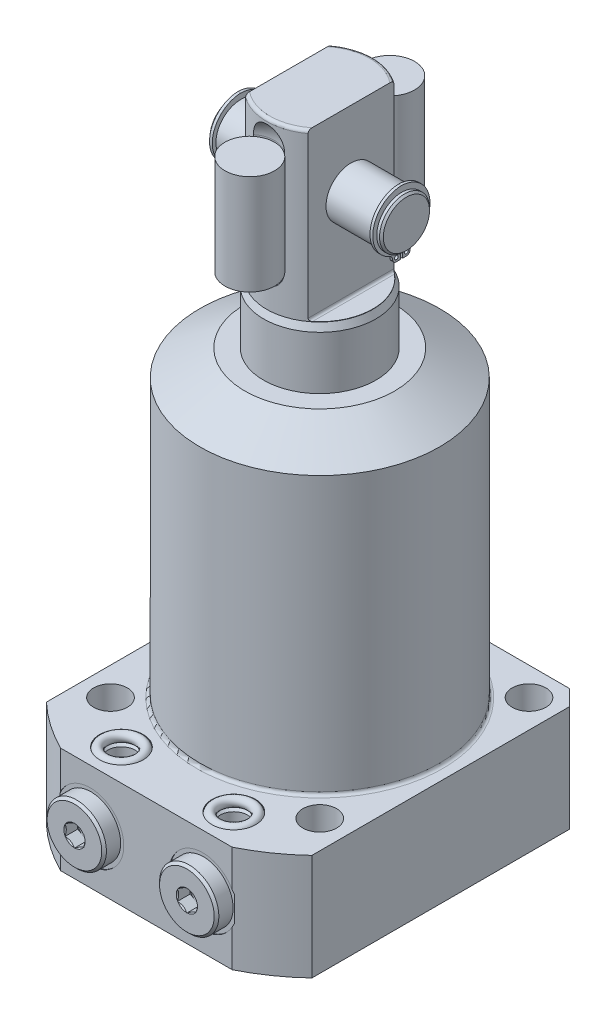
SolidWorks part; units mm, degrees
material "AISI 1020"
ref_plane "Front Plane" through (0, 0, 0) normal (0, 0, 1) x (1, 0, 0)
ref_plane "Top Plane" through (0, 0, 0) normal (0, 1, 0) x (1, 0, 0)
ref_plane "Right Plane" through (0, 0, 0) normal (1, 0, 0) x (0, 0, -1)
sketch "Sketch1" plane through (0, 0, 0) normal (0, 0, 1) x (1, 0, 0)
  line L0 (18, 0) -> (18, 114)
  line L1 (18, 114) -> (17, 116.1445)
  line L2 (17, 116.1445) -> (17, 168.25)
  line L3 (16, 169.25) -> (0, 169.25)
  line L4 (0, 61.9815) -> (0, 93.5758) construction
  line L8 (0, -3.075) -> (0, 64.575) construction
  line L9 (18, 0) -> (0, 0)
  line L10 (0, 0) -> (0, 169.25)
  line L11 (-25.0821, -34) -> (21.8096, -34) construction
  arc A0 (17, 168.25) -> (16, 169.25) centre (16, 168.25) ccw
  dimension "D1" = 1
  dimension "D2" = 36
  dimension "D3" = 34
  dimension "D4" = 55.25
  dimension "D5" = 34
  dimension "D6" = 25
  dimension "D7" = 203.25
revolve "PLUNGER" add sketch "Sketch1" angle 360 about L8
ref_plane "FLAT_SKTCH_PLN" through (0, 0, 0) normal (0, 0, 1) x (1, 0, 0)
sketch "Sketch17" plane through (0, 0, 0) normal (0, 0, 1) x (1, 0, 0)
  line L0 (16, 169.25) -> (-16, 169.25) construction
  line L1 (17, 116.1445) -> (17, 168.25) construction
  line L2 (16, 169.25) -> (-16, 169.25)
  line L3 (17, 116.1445) -> (17, 168.25)
  line L5 (10, 169.25) -> (17, 169.25)
  line L6 (10, 169.25) -> (10, 117.05)
  line L7 (10.8, 116.25) -> (17, 116.25)
  line L8 (17, 169.25) -> (17, 116.25)
  line L9 (0, 168.25) -> (0, 116.1445) construction
  line L10 (0, 57.0947) -> (0, 92.2162) construction
  line L11 (0, 114) -> (0, 0) construction
  line L12 (0, 114) -> (0, 116.1445) construction
  line L13 (-17, 169.25) -> (-17, 116.25)
  line L14 (-10.8, 116.25) -> (-17, 116.25)
  line L15 (-10, 169.25) -> (-10, 117.05)
  line L16 (-10, 169.25) -> (-17, 169.25)
  line L17 (-17, 116.1445) -> (-17, 168.25)
  arc A0 (10, 117.05) -> (10.8, 116.25) centre (10.8, 117.05) ccw
  arc A1 (-10, 117.05) -> (-10.8, 116.25) centre (-10.8, 117.05) cw
  dimension "D3" = 0.8
  dimension "D1" = 53
  dimension "D2" = 20
extrude "FLATS" cut sketch "Sketch17" against normal mid plane 100 contours L6 A0 L7 L8 L5 | L13 L14 A1 L15 L16
sketch "Sketch22" plane through (0, 0, 0) normal (0, 0, 1) x (1, 0, 0)
  line L0 (-11.5689, 145.25) -> (12.3381, 145.25) construction
  line L1 (0, 87.9433) -> (0, 65.5754) construction
  line L2 (0, 172.8601) -> (0, 160.5297) construction
  line L3 (0, 168.25) -> (0, 116.1445) construction
  line L4 (10, 169.25) -> (-10, 169.25) construction
  line L5 (10, 169.25) -> (-10, 169.25)
  line L6 (27.75, 152.65) -> (27.15, 153.25)
  line L7 (27.15, 153.25) -> (26.25, 153.25)
  line L8 (27.75, 152.65) -> (27.75, 145.25)
  line L9 (27.75, 145.25) -> (-27.75, 145.25)
  line L11 (26.25, 153.25) -> (26.25, 152.7175)
  line L12 (26.25, 152.7175) -> (25.25, 152.7175)
  line L13 (25.25, 152.7175) -> (25.25, 153.25)
  line L14 (25.25, 153.25) -> (-25.25, 153.25)
  line L15 (-25.25, 152.7175) -> (-25.25, 153.25)
  line L16 (-26.25, 152.7175) -> (-25.25, 152.7175)
  line L17 (-26.25, 153.25) -> (-26.25, 152.7175)
  line L18 (-27.75, 152.65) -> (-27.75, 145.25)
  line L19 (-27.15, 153.25) -> (-26.25, 153.25)
  line L20 (-27.75, 152.65) -> (-27.15, 153.25)
  dimension "D1" = 24
  dimension "D2" = 45
  dimension "D3" = 0.6
  dimension "D4" = 16
  dimension "D5" = 1
  dimension "D6" = 14.935
  dimension "D7" = 55.5
  dimension "D8" = 50.5
revolve "PIVOT_PIN" add sketch "Sketch22" angle 360 about L0
sketch "Sketch23" plane through (25.25, 0, 0) normal (1, 0, 0) x (0, 0, -1)
  line L0 (0, 79.466) -> (0, 70.8639) construction
  line L1 (0, 168.25) -> (0, 116.1445) construction
  line L2 (0, 145.25) -> (-4.1358, 135.8979) construction
  line L3 (-0.35, 134.7079) -> (-1.61, 134.7079)
  line L4 (0, 145.25) -> (4.1358, 135.8979) construction
  line L5 (0.35, 137.5079) -> (0.35, 134.7079)
  line L6 (-0.35, 137.5079) -> (-0.35, 134.7079)
  line L7 (0.35, 134.7079) -> (1.61, 134.7079)
  arc A0 (0.35, 137.5079) -> (-0.35, 137.5079) centre (0, 145.25) ccw
  arc A1 (-2.8, 135.8979) -> (-1.61, 134.7079) centre (-1.61, 135.8979) ccw
  arc A2 (-2.8, 135.8979) -> (-3.5955, 137.1195) centre (-4.1358, 135.8979) ccw
  arc A3 (-3.5955, 137.1195) -> (0, 155.03) centre (0.1884, 145.676) cw
  circle A4 centre (-1.61, 135.8979) radius 0.595
  circle A5 centre (1.61, 135.8979) radius 0.595
  arc A6 (3.5955, 137.1195) -> (0, 155.03) centre (-0.1884, 145.676) ccw
  arc A7 (2.8, 135.8979) -> (3.5955, 137.1195) centre (4.1358, 135.8979) cw
  arc A8 (2.8, 135.8979) -> (1.61, 134.7079) centre (1.61, 135.8979) cw
  point P17 (-3.1344, 138.1621)
  point P27 (3.1344, 138.1621)
  point P28 (0, 153)
  dimension "D1" = 15.5
  dimension "D3" = 1.19
  dimension "D8" = 1.19
  dimension "D2" = 0.7
  dimension "D4" = 2.8
  dimension "D5" = 2.8
  dimension "D6" = 2.03
  dimension "D7" = 1.14
extrude "RETAINING_RING" add sketch "Sketch23" along normal blind 0.89
ref_plane "PIN_CL" through (0, 0, 0) normal (-1, 0, 0) x (0, 0, 1)
mirror "RETAINING_RING-OPP" about plane through (0, 0, 0) normal (-1, 0, 0) of "RETAINING_RING"
sketch "Sketch20" plane through (0, 0, 0) normal (-1, 0, 0) x (0, 0, 1)
  line L0 (-12.49, 169.25) -> (12.49, 169.25) construction
  line L1 (-12.49, 169.25) -> (12.49, 169.25)
  line L2 (0, 87.5232) -> (0, 65.9324) construction
  line L3 (0, 172.858) -> (0, 160.534) construction
  line L4 (0, 168.25) -> (0, 116.1445) construction
  line L5 (22.4375, 82.048) -> (22.4375, 54.8595) construction
  line L6 (14.5, 161.75) -> (14.5, 128.75)
  line L7 (22.4375, 169.6875) -> (22.4375, 120.8125)
  arc A0 (22.4375, 169.6875) -> (14.5, 161.75) centre (22.4375, 161.75) ccw
  arc A1 (14.5, 128.75) -> (22.4375, 120.8125) centre (22.4375, 128.75) ccw
  dimension "D3" = 33
  dimension "D1" = 14.5
  dimension "D2" = 15.875
  dimension "D4" = 7.5
revolve "SPRING_SLOT" cut sketch "Sketch20" angle 360 about L5
mirror "SPRING_SLOT_OPP" about plane through (0, 0, 0) normal (0, 0, 1) of "SPRING_SLOT"
sketch "Sketch24" plane through (0, 0, 0) normal (-1, 0, 0) x (0, 0, 1)
  line L0 (7.2759, 145.25) -> (-10.8708, 145.25) construction
  line L1 (-22.4075, 84.5678) -> (-22.4075, 68.6953) construction
  line L2 (-14.5, 128.75) -> (-14.5, 161.75) construction
  line L3 (-14.47, 161.25) -> (-22.4075, 161.25)
  line L4 (-14.47, 161.25) -> (-14.47, 129.25)
  line L6 (-22.4075, 161.25) -> (-22.4075, 129.25)
  line L7 (-14.47, 129.25) -> (-22.4075, 129.25)
  dimension "D1" = 15.875
  dimension "D2" = 32
  dimension "D3" = 0.03
revolve "SPRING" add sketch "Sketch24" angle 360 about L1
mirror "SPRING_OPP" about plane through (0, 0, 0) normal (0, 0, 1) of "SPRING"
sketch "Sketch6" plane through (0, 0, 0) normal (0, 0, 1) x (1, 0, 0)
  line L0 (0, -34) -> (0, 67.6291) construction
  line L1 (0, 97) -> (24, 97)
  line L2 (24, 97) -> (38.385, 88.6948)
  line L3 (61.915, 0) -> (61.915, -34)
  line L4 (0, -34) -> (61.915, -34)
  line L5 (38.385, 0) -> (38.385, 88.6948)
  line L6 (61.915, 0) -> (38.385, 0)
  line L7 (0, -34) -> (0, 97)
  dimension "D1" = 76.77
  dimension "D2" = 34
  dimension "D3" = 131
  dimension "D4" = 123.83
  dimension "D5" = 30
  dimension "D6" = 48
revolve "BODY_REVOLVE" add sketch "Sketch6" angle 360 about L0
sketch "Sketch7" plane through (0, 0, 0) normal (0, 1, 0) x (-1, 0, 0)
  line L0 (0, 0) -> (0, -52.3237) construction
  line L1 (-42.5, 55.5) -> (42.5, 55.5)
  line L2 (-42.5, 55.5) -> (-42.5, -42.5)
  line L3 (-42.5, -42.5) -> (42.5, -42.5)
  line L4 (42.5, 55.5) -> (42.5, -42.5)
  dimension "D1" = 85
  dimension "D2" = 98
  dimension "D3" = 42.5
extrude "FLANGE_SIDES" cut sketch "Sketch7" against normal through all flip side to cut
sketch "Sketch8" plane through (0, -34, 0) normal (0, -1, 0) x (1, 0, 0)
  circle A0 centre (-33.5, 33.5) radius 5.4
  dimension "D1" = 10.8
  dimension "D2" = 33.5
  dimension "D3" = 33.5
extrude "MOUNTING HOLES" cut sketch "Sketch8" against normal through all
pattern_circular "MOUNTING_PATTERN" count 4 over 360 about axis through (0, 0, 0) along (0, 1, 0) of "MOUNTING HOLES"
chamfer "FLANGE_CHAMFER" distance 5 angle 45 2 edges at (-42.5, -17, -42.5) (42.5, -17, -42.5)
fillet "BODY_FILLET" radius 1 1 edges at (38.385, 0, 0)
ref_plane "FLANGE-PORT_PLANE" through (0, -17, 0) normal (0, -1, 0) x (1, 0, 0)
sketch "Sketch11" plane through (0, -17, 0) normal (0, -1, 0) x (1, 0, 0)
  line L0 (-18, 42.9716) -> (-18, 19.7499) construction
  line L1 (-28.75, 55.5) -> (-28.75, 55.25)
  line L3 (-28.75, 55.25) -> (-24.65, 55.25)
  line L4 (-24.65, 55.25) -> (-23.945, 54.545)
  line L5 (-23.945, 54.545) -> (-23.945, 36.53)
  line L6 (-23.945, 36.53) -> (-18, 36.53)
  line L7 (-18, 36.53) -> (-18, 55.5)
  line L8 (-18, 55.5) -> (-28.75, 55.5)
  line L10 (27.4448, 55.5) -> (-27.4448, 55.5) construction
  dimension "D1" = 18
  dimension "D2" = 0.25
  dimension "D3" = 11.89
  dimension "D4" = 18.72
  dimension "D5" = 21.5
  dimension "D6" = 45
  dimension "D7" = 0.705
revolve "PORT SPOT FACE" cut sketch "Sketch11" angle 360 about L0
ref_plane "MANIFOLD_PORT_PLANE" through (0, 0, 45.5) normal (0, 0, 1) x (1, 0, 0)
sketch "Sketch13" plane through (0, 0, 45.5) normal (0, 0, 1) x (1, 0, 0)
  line L0 (-22.375, -22) -> (-22.375, -31)
  line L1 (-22.375, -31) -> (-23.125, -31.75)
  line L2 (-23.125, -31.75) -> (-25, -31.75)
  line L3 (-25, -31.75) -> (-25, -34)
  line L5 (-25, -34) -> (-18, -34)
  line L6 (-18, -34) -> (-18, -22)
  line L7 (-18, -22) -> (-22.375, -22)
  line L8 (-18, 15.2099) -> (-18, -4.3918) construction
  line L10 (27.4448, -34) -> (-27.4448, -34) construction
  dimension "D1" = 18
  dimension "D2" = 8.75
  dimension "D3" = 12
  dimension "D4" = 2.25
  dimension "D5" = 14
  dimension "D6" = 45
  dimension "D7" = 0.75
revolve "BOTTOM_MANIFOLD_PORT" cut sketch "Sketch13" angle 360 about L8
sketch "Sketch14" plane through (0, -17, 0) normal (0, -1, 0) x (1, 0, 0)
  line L0 (-18, 32.5881) -> (-18, 43.5576) construction
  line L1 (-18, 36.53) -> (-18, 54.545) construction
  line L2 (-21.4, 60.55) -> (-26.75, 60.55)
  line L3 (-26.75, 60.55) -> (-27.5, 59.8)
  line L4 (-27.5, 59.8) -> (-27.5, 55.25)
  line L5 (-7.25, 55.25) -> (-27.9447, 55.25) construction
  line L6 (-27.5, 55.25) -> (-22.125, 55.25)
  line L7 (-11.35, 55.25) -> (-24.65, 55.25) construction
  line L8 (-22.125, 55.25) -> (-22.125, 52.7472)
  line L9 (-22.125, 52.7472) -> (-18, 52.7472)
  line L10 (-18, 52.7472) -> (-18, 52.7482)
  line L11 (-18, 52.7482) -> (-21, 54.5508)
  line L12 (-21, 54.5508) -> (-21, 60.15)
  line L13 (-21, 60.15) -> (-21.4, 60.55)
  dimension "D1" = 8.25
  dimension "D2" = 2.5028
  dimension "D3" = 59
  dimension "D4" = 6
  dimension "D5" = 5.3
  dimension "D6" = 19
  dimension "D7" = 45
  dimension "D8" = 0.75
  dimension "D9" = 45
  dimension "D10" = 0.4
  dimension "D11" = 0.001
revolve "BSPP_PLUGHEAD" add sketch "Sketch14" angle 360 about L0
sketch "Sketch15" plane through (0, 0, 60.55) normal (0, 0, 1) x (1, 0, 0)
  line L1 (-15, -18.7321) -> (-15, -15.2679)
  line L2 (-15, -15.2679) -> (-18, -13.5359)
  line L3 (-18, -13.5359) -> (-21, -15.2679)
  line L4 (-21, -15.2679) -> (-21, -18.7321)
  line L5 (-21, -18.7321) -> (-18, -20.4641)
  line L6 (-18, -20.4641) -> (-15, -18.7321)
  circle A0 centre (-18, -17) radius 3 construction
  dimension "D1" = 6
extrude "BSPP_PLUG_HEX" cut sketch "Sketch15" against normal blind 4.06
mirror "MANIFOLD_TOP_MIRROR" about plane through (0, -17, 0) normal (0, -1, 0) of "BOTTOM_MANIFOLD_PORT"
mirror "BSPP-MANIFOLD_MIRROR" about plane through (0, 0, 0) normal (1, 0, 0) of "MANIFOLD_TOP_MIRROR", "PORT SPOT FACE", "BOTTOM_MANIFOLD_PORT", "BSPP_PLUGHEAD", "BSPP_PLUG_HEX"
sketch "Sketch16" plane through (0, 0, 45.5) normal (0, 0, 1) x (1, 0, 0)
  line L1 (-18, 9.3219) -> (-18, -15.1063) construction
  line L2 (-18, -31) -> (-18, -22) construction
  line L3 (27.4448, -34) -> (-27.4448, -34) construction
  circle A0 centre (-23.5, -33.25) radius 1.5
  dimension "D1" = 3
  dimension "D3" = 0.75
  dimension "D2" = 11
revolve "MANIFOLD_O-RING" add sketch "Sketch16" angle 360 about L1
mirror "MANIFOLD_O-RING_MIRROR" about plane through (0, 0, 0) normal (1, 0, 0) of bodies 128
mirror "MANIFOLD_O-RING_MIRROR_TOP" about plane through (0, -17, 0) normal (0, -1, 0) of bodies 128 130
